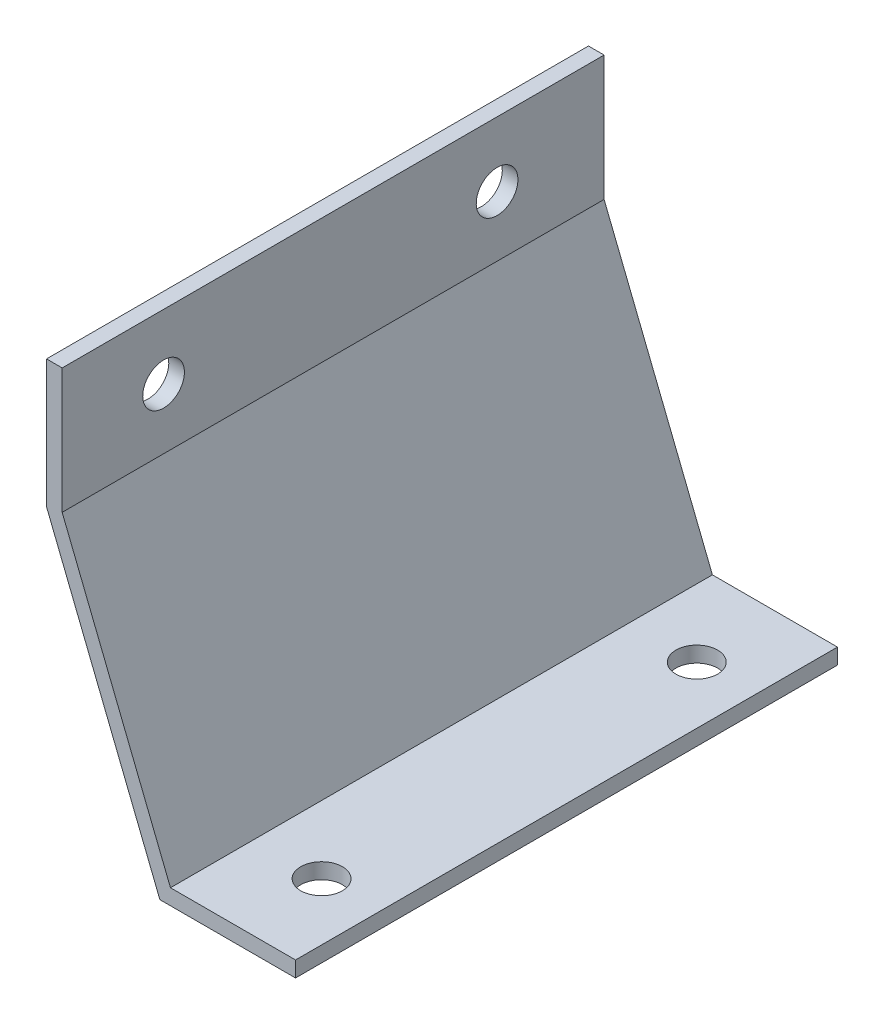
SolidWorks part; units mm, degrees
ref_plane "Front Plane" through (0, 0, 0) normal (0, 0, 1) x (1, 0, 0)
ref_plane "Top Plane" through (0, 0, 0) normal (0, 1, 0) x (1, 0, 0)
ref_plane "Right Plane" through (0, 0, 0) normal (1, 0, 0) x (0, 0, -1)
sketch "Sketch1" plane through (0, 0, 0) normal (0, 0, 1) x (1, 0, 0)
  line L0 (0, 120.65) -> (0, 82.55)
  line L1 (0, 82.55) -> (32.9956, 0)
  line L2 (32.9956, 0) -> (71.0956, 0)
  dimension "D1" = 38.1
  dimension "D2" = 38.1
  dimension "D3" = 82.55
  dimension "D4" = 88.9
extrude "Extrude-Thin1" add sketch "Sketch1" along normal blind 165.1 thin
sketch "Sketch2" plane through (0, 0, 0) normal (1, 0, 0) x (0, 0, -1)
  circle A0 centre (-134.2049, 100.9423) radius 6.35
  circle A1 centre (-32.6049, 100.9423) radius 6.35
  dimension "D1" = 12.7
  dimension "D2" = 12.7
  dimension "D3" = 101.6
extrude "Cut-Extrude1" cut sketch "Sketch2" against normal through all
sketch "Sketch3" plane through (0, 0, 0) normal (0, 1, 0) x (1, 0, 0)
  line L3 (71.0956, -165.1) -> (71.0956, 0) construction
  line L4 (32.9956, 0) -> (71.0956, 0) construction
  line L5 (32.9956, -165.1) -> (71.0956, -165.1) construction
  circle A1 centre (53.6331, -25.4) radius 6.35
  circle A2 centre (53.6331, -139.7) radius 6.35
  dimension "D3" = 12.7
  dimension "D1" = 17.4625
  dimension "D5" = 12.7
  dimension "D2" = 25.4
  dimension "D4" = 25.4
extrude "Cut-Extrude2" cut sketch "Sketch3" against normal through all
